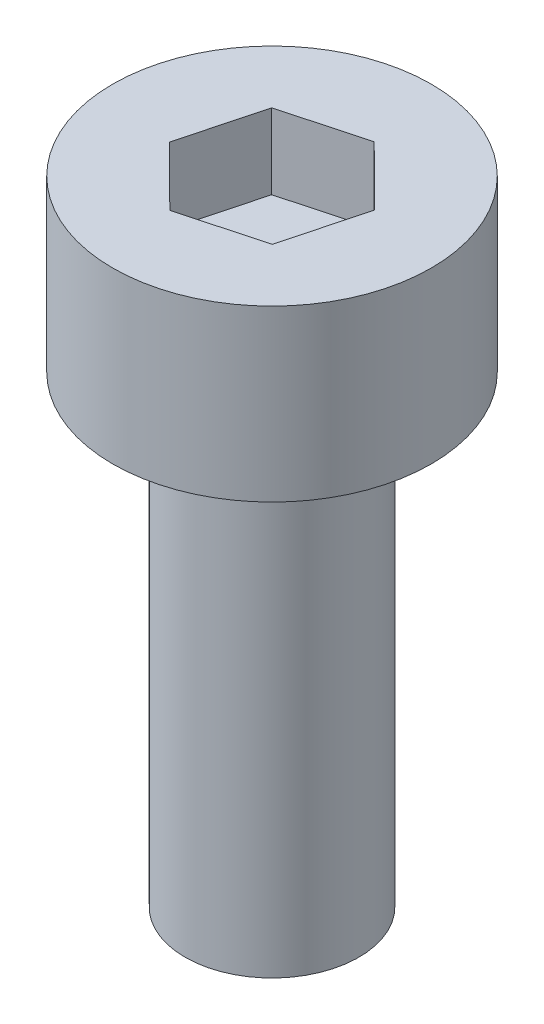
SolidWorks part; units mm, degrees
ref_plane "前视基准面" through (0, 0, 0) normal (0, 0, 1) x (1, 0, 0)
ref_plane "上视基准面" through (0, 0, 0) normal (0, 1, 0) x (1, 0, 0)
ref_plane "右视基准面" through (0, 0, 0) normal (1, 0, 0) x (0, 0, -1)
sketch "草图1" plane through (0, 0, 0) normal (0, 1, 0) x (1, 0, 0)
  circle A0 centre (0, 0) radius 1.5
  dimension "D1" = 3
extrude "凸台-拉伸1" add sketch "草图1" along normal blind 8
sketch "草图2" plane through (0, 8, 0) normal (0, 1, 0) x (1, 0, 0)
  circle A0 centre (0, 0) radius 2.75
  dimension "D1" = 5.5
extrude "凸台-拉伸2" add sketch "草图2" along normal blind 2.93
sketch "草图3" plane through (0, 10.93, 0) normal (0, 1, 0) x (1, 0, 0)
  line L1 (1.024, -1.0172) -> (1.3929, 0.3782)
  line L2 (1.3929, 0.3782) -> (0.3689, 1.3954)
  line L3 (0.3689, 1.3954) -> (-1.024, 1.0172)
  line L4 (-1.024, 1.0172) -> (-1.3929, -0.3782)
  line L5 (-1.3929, -0.3782) -> (-0.3689, -1.3954)
  line L6 (-0.3689, -1.3954) -> (1.024, -1.0172)
  circle A0 centre (0, 0) radius 1.25 construction
  dimension "D1" = 2.5
extrude "切除-拉伸1" cut sketch "草图3" against normal blind 1.3
